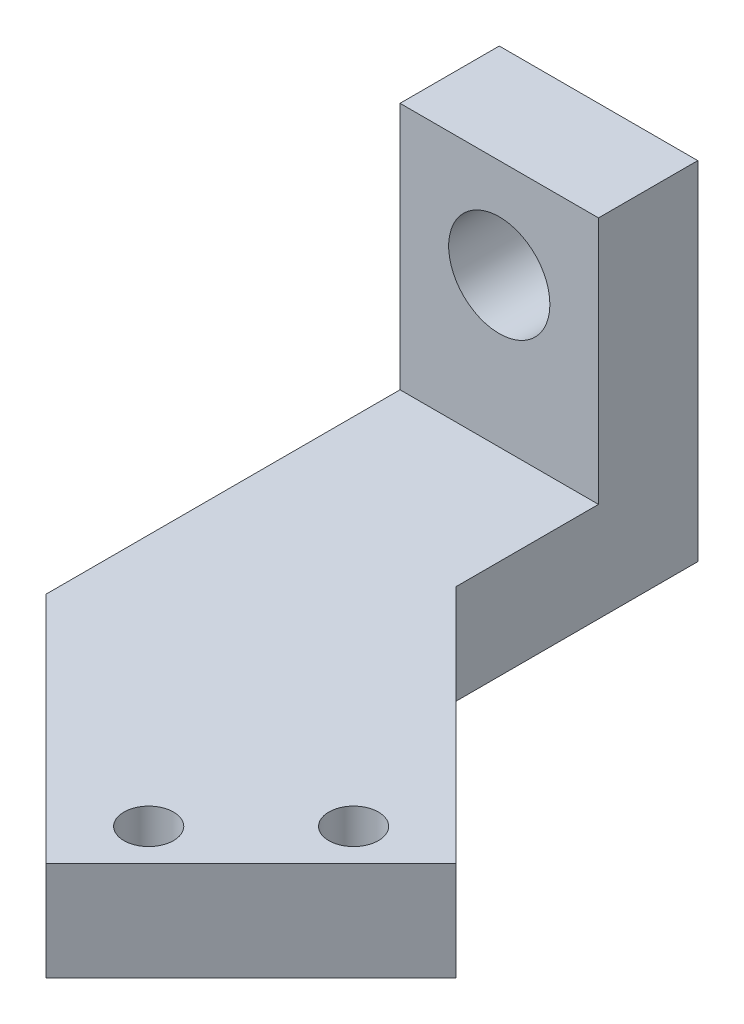
SolidWorks part; units mm, degrees
ref_plane "Front Plane" through (0, 0, 0) normal (0, 0, 1) x (1, 0, 0)
ref_plane "Top Plane" through (0, 0, 0) normal (0, 1, 0) x (1, 0, 0)
ref_plane "Right Plane" through (0, 0, 0) normal (1, 0, 0) x (0, 0, -1)
sketch "Sketch1" plane through (0, 0, 0) normal (0, 0, 1) x (1, 0, 0)
  line L0 (-10, -10) -> (-10, -15)
  line L1 (10, -10) -> (-10, -10) construction
  line L2 (10, -10) -> (10, 10)
  line L3 (10, 10) -> (-10, 10)
  line L4 (-10, -10) -> (-10, 10)
  line L5 (10, -10) -> (-10, 10) construction
  line L6 (10, 10) -> (-10, -10) construction
  line L7 (-10, -15) -> (10, -15)
  line L8 (10, -15) -> (10, -10)
  circle A0 centre (0, 0) radius 5.1
  dimension "D1" = 10.2
  dimension "D2" = 10
  dimension "D3" = 10
  dimension "D4" = 5
extrude "Boss-Extrude1" add sketch "Sketch1" along normal blind 10
sketch "Sketch4" plane through (0, -15, 0) normal (0, -1, 0) x (1, 0, 0)
  line L0 (-10, 10) -> (-10, 0)
  line L1 (-10, 0) -> (10, 0)
  line L2 (10, 0) -> (10, 10)
  line L4 (0, 10) -> (0, 35) construction
  line L5 (-12.5, 35) -> (12.5, 35) construction
  line L6 (-10, 10) -> (-14.5, 35)
  line L7 (-14.5, 35) -> (-14.5, 40)
  line L8 (-14.5, 40) -> (14.5, 40)
  line L9 (14.5, 40) -> (14.5, 35)
  line L10 (14.5, 35) -> (10, 10)
  line L11 (-10, 10) -> (10, 10) construction
  point P13 (0, 35)
  point P14 (-10, 10)
  point P19 (-10, 10)
  point P20 (0, 10)
  dimension "D1" = 25
  dimension "D2" = 25
  dimension "D3" = 2
  dimension "D4" = 2
  dimension "D5" = 5
extrude "Boss-Extrude3" add sketch "Sketch4" along normal blind 10
sketch "Sketch6" plane through (0, -15, 0) normal (0, 1, 0) x (1, 0, 0)
  line L0 (-14.5, -35) -> (14.5, -35) construction
  line L1 (0, -35) -> (0, -40) construction
  line L2 (14.5, -40) -> (-14.5, -40) construction
  line L3 (0, -35) -> (23.8295, -58.8295) construction
  line L4 (0, -35) -> (10.3238, -24.6762)
  line L5 (10.3238, -24.6762) -> (34.1533, -48.5057)
  line L6 (34.1533, -48.5057) -> (13.5057, -69.1533)
  line L7 (13.5057, -69.1533) -> (-10.3238, -45.3238)
  line L8 (-10.3238, -45.3238) -> (0, -35) construction
  line L9 (-14.5, -40) -> (-10.3238, -45.3238)
  line L10 (-14.5, -40) -> (-5, -40)
  line L11 (-5, -40) -> (0, -35)
  dimension "D1" = 45
  dimension "D2" = 29.2
  dimension "D3" = 33.7
extrude "Boss-Extrude4" add sketch "Sketch6" against normal blind 10
sketch "Sketch7" plane through (0, -15, 0) normal (0, 1, 0) x (1, 0, 0)
  line L0 (13.5057, -69.1533) -> (7.0357, -62.6832) construction
  line L1 (-10.3238, -45.3238) -> (13.5057, -69.1533) construction
  line L2 (7.0357, -62.6832) -> (27.6832, -42.0357) construction
  line L3 (34.1533, -48.5057) -> (13.1505, -27.503) construction
  line L4 (27.6832, -42.0357) -> (34.1533, -48.5057) construction
  line L5 (34.1533, -48.5057) -> (13.5057, -69.1533) construction
  line L6 (17.3595, -52.3595) -> (23.8295, -58.8295) construction
  line L7 (10.2707, -65.9182) -> (20.5945, -55.5945) construction
  line L8 (20.5945, -55.5945) -> (30.9182, -45.2707) construction
  circle A0 centre (15.4326, -60.7564) radius 2.5
  circle A1 centre (25.7564, -50.4326) radius 2.5
  dimension "D2" = 5
  dimension "D3" = 5
  dimension "D1" = 9.15
extrude "Cut-Extrude1" cut sketch "Sketch7" against normal up to next
sketch "Sketch8" plane through (0, -25, 0) normal (0, -1, 0) x (1, 0, 0)
  line L3 (10, 10) -> (10, 24.3525)
  line L4 (13.1505, 27.503) -> (10, 24.3525)
  line L5 (34.1533, 48.5057) -> (13.1505, 27.503) construction
  line L6 (13.1505, 27.503) -> (10, 10)
  line L7 (-14.5, 40) -> (-14.5, 35)
  line L8 (-14.5, 35) -> (-10, 10) construction
  line L9 (-14.5, 35) -> (-10, 10)
  line L10 (-14.5, 40) -> (-10.3238, 45.3238)
  line L11 (-10, 10) -> (-10, 45.6475)
  line L12 (-10.3238, 45.3238) -> (13.5057, 69.1533) construction
  line L13 (-10, 45.6475) -> (-10.3238, 45.3238)
extrude "Cut-Extrude4" cut sketch "Sketch8" against normal up to next
